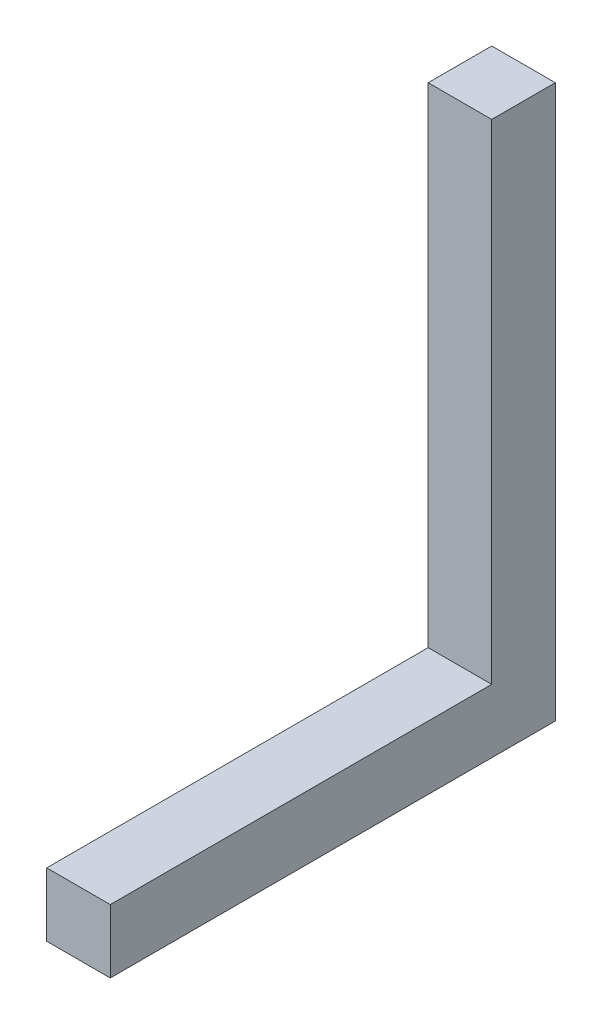
SolidWorks part; units mm, degrees
ref_plane "Front Plane" through (0, 0, 0) normal (0, 0, 1) x (1, 0, 0)
ref_plane "Top Plane" through (0, 0, 0) normal (0, 1, 0) x (1, 0, 0)
ref_plane "Right Plane" through (0, 0, 0) normal (1, 0, 0) x (0, 0, -1)
sketch "Sketch1" plane through (0, 0, 0) normal (0, 0, 1) x (1, 0, 0)
  line L1 (5.75, 5.75) -> (-5.75, 5.75)
  line L2 (5.75, 5.75) -> (5.75, -5.75)
  line L3 (5.75, -5.75) -> (-5.75, -5.75)
  line L4 (-5.75, 5.75) -> (-5.75, -5.75)
  line L5 (5.75, 5.75) -> (-5.75, -5.75) construction
  line L6 (5.75, -5.75) -> (-5.75, 5.75) construction
  point P0 (0, 0)
  dimension "D1" = 11.5
  dimension "D2" = 11.5
extrude "Boss-Extrude1" add sketch "Sketch1" along normal blind 69
sketch "Sketch3" plane through (0, 0, 0) normal (0, 1, 0) x (1, 0, 0)
  line L1 (5.75, 0) -> (-5.75, 0)
  line L2 (5.75, 0) -> (5.75, 11.5)
  line L3 (5.75, 11.5) -> (-5.75, 11.5)
  line L4 (-5.75, 0) -> (-5.75, 11.5)
  dimension "D1" = 11.5
  dimension "D2" = 11.5
extrude "Boss-Extrude2" add sketch "Sketch3" along normal blind 100 from surface at -5.75 starting at face at (0, -5.75, 34.5)
